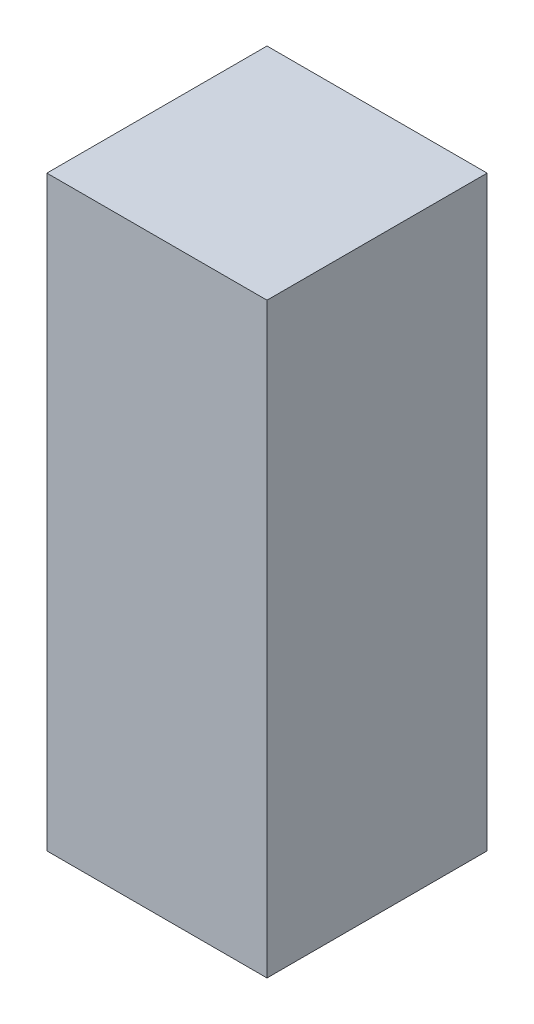
SolidWorks part; units mm, degrees
material "Oak"
ref_plane "Front Plane" through (0, 0, 0) normal (0, 0, 1) x (1, 0, 0)
ref_plane "Top Plane" through (0, 0, 0) normal (0, 1, 0) x (1, 0, 0)
ref_plane "Right Plane" through (0, 0, 0) normal (1, 0, 0) x (0, 0, -1)
sketch "Sketch1" plane through (0, 0, 0) normal (0, 1, 0) x (1, 0, 0)
  line L1 (-9.525, -9.525) -> (9.525, -9.525)
  line L2 (-9.525, -9.525) -> (-9.525, 9.525)
  line L3 (-9.525, 9.525) -> (9.525, 9.525)
  line L4 (9.525, -9.525) -> (9.525, 9.525)
  line L5 (-9.525, -9.525) -> (9.525, 9.525) construction
  line L6 (-9.525, 9.525) -> (9.525, -9.525) construction
  point P0 (0, 0)
  dimension "D1" = 19.05
extrude "Boss-Extrude1" add sketch "Sketch1" along normal blind 50.8
